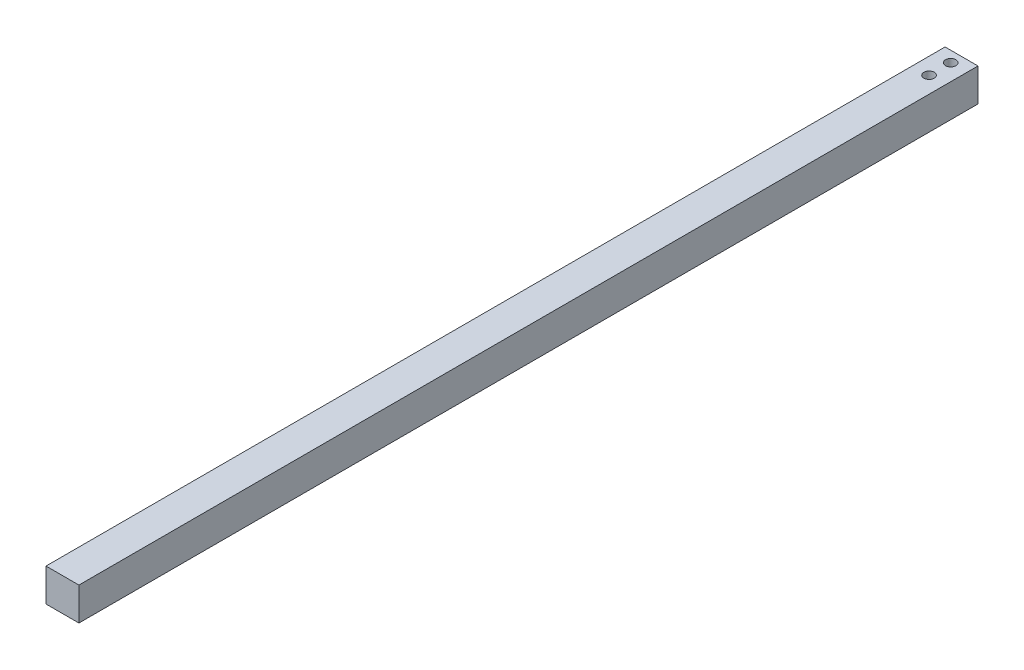
SolidWorks part; units mm, degrees
ref_plane "Front Plane" through (0, 0, 0) normal (0, 0, 1) x (1, 0, 0)
ref_plane "Top Plane" through (0, 0, 0) normal (0, 1, 0) x (1, 0, 0)
ref_plane "Right Plane" through (0, 0, 0) normal (1, 0, 0) x (0, 0, -1)
sketch "Sketch1" plane through (0, 0, 0) normal (0, 0, 1) x (1, 0, 0)
  line L1 (-9.5, -9.5) -> (9.5, -9.5)
  line L2 (-9.5, -9.5) -> (-9.5, 9.5)
  line L3 (-9.5, 9.5) -> (9.5, 9.5)
  line L4 (9.5, -9.5) -> (9.5, 9.5)
  line L5 (-9.5, -9.5) -> (9.5, 9.5) construction
  line L6 (-9.5, 9.5) -> (9.5, -9.5) construction
  point P0 (0, 0)
extrude "Boss-Extrude1" add sketch "Sketch1" along normal blind 519
sketch "Sketch2" plane through (0, -9.5, 0) normal (0, -1, 0) x (1, 0, 0)
  line L0 (-9.5, 519) -> (9.5, 519) construction
  line L1 (-9, 511.5) -> (9, 511.5)
  line L2 (-9, 511.5) -> (-9, 526.5)
  line L3 (-9, 526.5) -> (9, 526.5)
  line L4 (9, 511.5) -> (9, 526.5)
  line L5 (-9, 511.5) -> (9, 526.5) construction
  line L6 (-9, 526.5) -> (9, 511.5) construction
  line L7 (9, 519) -> (9, 511.5)
  line L8 (9, 511.5) -> (9, 515.25)
  line L9 (9, 515.25) -> (-9, 515.25)
  line L10 (9, 515.25) -> (6, 515.25)
  line L11 (0, 519) -> (0, 511.5)
  circle A0 centre (6, 515.25) radius 2
  circle A1 centre (-6, 515.25) radius 2
  point P0 (0, 519)
extrude "Cut-Extrude1" cut sketch "Sketch2" against normal blind 9 contours A1 L9 | A1 L9 | L10 A0 L9 | L9 A0 L10
sketch "Sketch3" plane through (0, 9.5, 0) normal (0, 1, 0) x (1, 0, 0)
  line L0 (9.5, 0) -> (-9.5, 0) construction
  line L1 (9.5, 0) -> (-9.5, 0)
  line L2 (0, 0) -> (0, -25)
  line L3 (0, -25) -> (0, -12.5)
  line L4 (0, -12.5) -> (-6.1481, -12.5)
  circle A0 centre (0, -18.75) radius 3
  circle A1 centre (0, -6.25) radius 3
extrude "Cut-Extrude2" cut sketch "Sketch3" against normal through all and the other way through all contours L3 A0 | A1 L2 | A1 L2 | L3 A0
